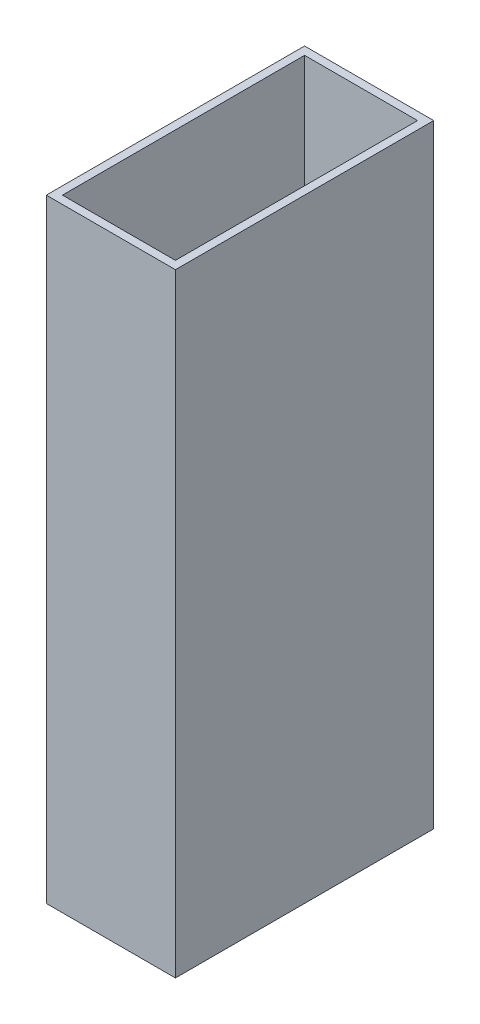
SolidWorks part; units mm, degrees
material "6061 Alloy"
ref_plane "Front Plane" through (0, 0, 0) normal (0, 0, 1) x (1, 0, 0)
ref_plane "Top Plane" through (0, 0, 0) normal (0, 1, 0) x (1, 0, 0)
ref_plane "Right Plane" through (0, 0, 0) normal (1, 0, 0) x (0, 0, -1)
sketch "Sketch1" plane through (0, 0, 0) normal (0, 1, 0) x (1, 0, 0)
  line L1 (-12.7, -25.4) -> (12.7, -25.4)
  line L2 (-12.7, -25.4) -> (-12.7, 25.4)
  line L3 (-12.7, 25.4) -> (12.7, 25.4)
  line L4 (12.7, -25.4) -> (12.7, 25.4)
  line L5 (-12.7, -25.4) -> (12.7, 25.4) construction
  line L6 (-12.7, 25.4) -> (12.7, -25.4) construction
  line L7 (-11.1125, -23.8125) -> (11.1125, -23.8125)
  line L8 (-11.1125, -23.8125) -> (-11.1125, 23.8125)
  line L9 (-11.1125, 23.8125) -> (11.1125, 23.8125)
  line L10 (11.1125, -23.8125) -> (11.1125, 23.8125)
  line L11 (-11.1125, -23.8125) -> (11.1125, 23.8125) construction
  line L12 (-11.1125, 23.8125) -> (11.1125, -23.8125) construction
  point P0 (0, 0)
  point P6 (0, 0)
  dimension "D1" = 50.8
  dimension "D2" = 25.4
  dimension "D3" = 1.5875
  dimension "D4" = 1.5875
extrude "Boss-Extrude1" add sketch "Sketch1" along normal blind 120.65
